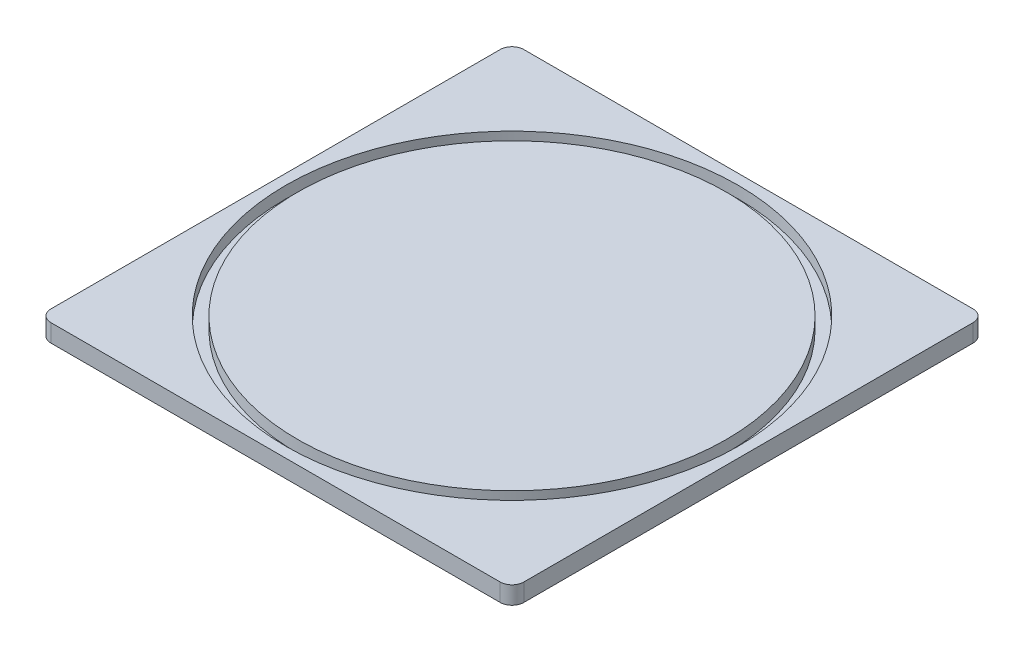
SolidWorks part; units mm, degrees
ref_plane "Front Plane" through (0, 0, 0) normal (0, 0, 1) x (1, 0, 0)
ref_plane "Top Plane" through (0, 0, 0) normal (0, 1, 0) x (1, 0, 0)
ref_plane "Right Plane" through (0, 0, 0) normal (1, 0, 0) x (0, 0, -1)
sketch "Sketch1" plane through (0, 0, 0) normal (0, 1, 0) x (1, 0, 0)
  line L0 (0, 40) -> (0, -40)
  line L1 (0, -40) -> (80, -40)
  line L2 (80, -40) -> (80, 40)
  line L3 (80, 40) -> (0, 40)
  dimension "D1" = 40
  dimension "D2" = 80
  dimension "D3" = 80
extrude "Boss-Extrude1" add sketch "Sketch1" along normal blind 3
sketch "Sketch3" plane through (0, 3, 0) normal (0, 1, 0) x (1, 0, 0)
  line L4 (80, -40) -> (80, 40) construction
  line L5 (0, -40) -> (80, -40) construction
  circle A0 centre (40, 0) radius 38.25
  dimension "D3" = 76.5
  dimension "D1" = 40
  dimension "D2" = 40
extrude "Cut-Extrude-Thin1" cut sketch "Sketch3" against normal blind 2 thin thin type one direction reverse wall 2
fillet "Fillet1" radius 2 4 edges at (0, 1.5, -40) (0, 1.5, 40) (80, 1.5, -40) (80, 1.5, 40)
